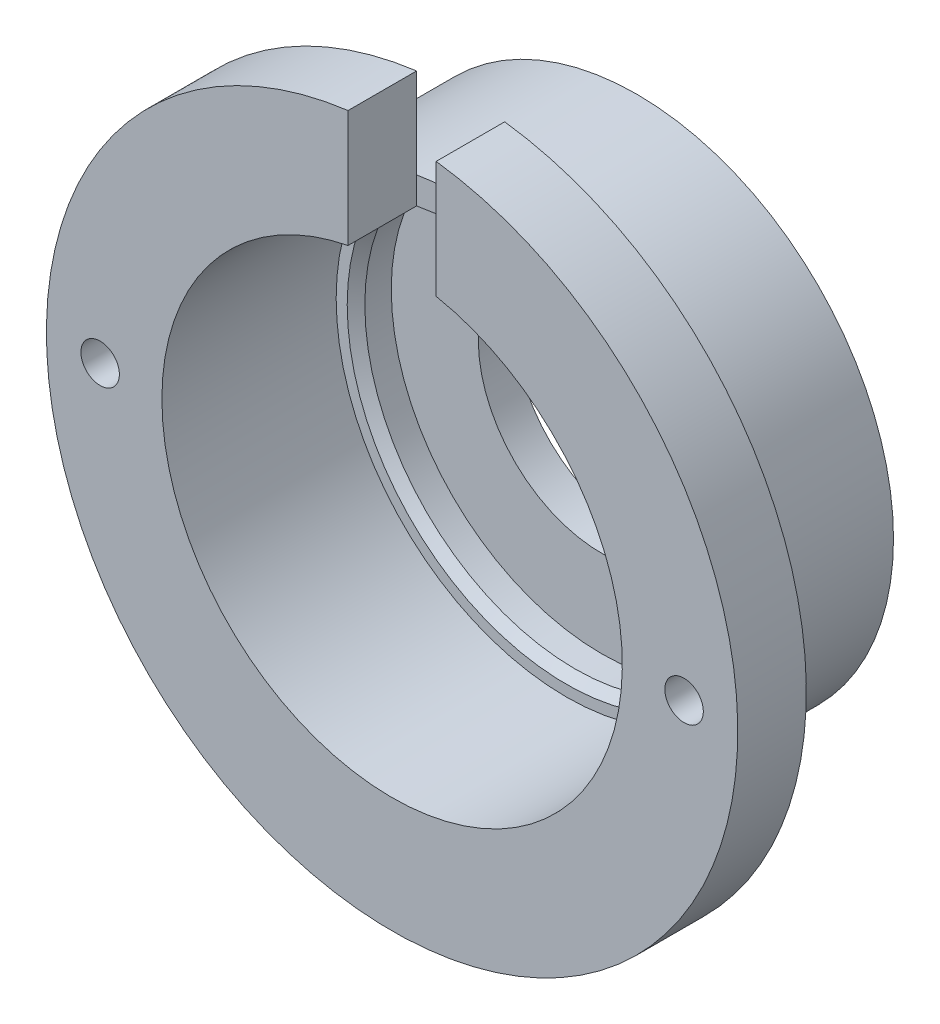
SolidWorks part; units mm, degrees
ref_plane "Front Plane" through (0, 0, 0) normal (0, 0, 1) x (1, 0, 0)
ref_plane "Top Plane" through (0, 0, 0) normal (0, 1, 0) x (1, 0, 0)
ref_plane "Right Plane" through (0, 0, 0) normal (1, 0, 0) x (0, 0, -1)
sketch "Sketch1" plane through (0, 0, 0) normal (0, 1, 0) x (1, 0, 0)
  line L0 (0, 25.4113) -> (0, -24.5124) construction
  line L2 (-7, 4.7005) -> (-19.6178, 4.7005)
  line L3 (-7, 4.7005) -> (-7, 2.7005)
  line L4 (-7, 2.7005) -> (-19.6178, 2.7005)
  line L5 (-19.6178, 4.7005) -> (-19.6178, 2.7005)
  line L6 (-11.938, 2.7005) -> (-19.6178, 2.7005)
  line L7 (-11.938, 2.7005) -> (-11.938, 0.7005)
  line L8 (-11.938, 0.7005) -> (-19.6178, 0.7005)
  line L9 (-19.6178, 2.7005) -> (-19.6178, 0.7005)
  line L10 (-13.0646, 0.7005) -> (-19.6178, 0.7005)
  line L11 (-13.0646, 0.7005) -> (-13.0646, -9.1895)
  line L12 (-13.0646, -9.1895) -> (-19.6178, -9.1895)
  line L13 (-19.6178, 0.7005) -> (-19.6178, -9.1895)
  dimension "D1" = 7
  dimension "D2" = 2
  dimension "D3" = 2
  dimension "D4" = 13.89
  dimension "D5" = 11.938
  dimension "D6" = 6.5532
revolve "Revolve1" add sketch "Sketch1" angle 360 about L0
sketch "Sketch2" plane through (0, 0, -4.7005) normal (0, 0, -1) x (-1, 0, 0)
  line L0 (19.6178, 0) -> (-19.6178, 0) construction
  line L1 (0, 19.4384) -> (0, -19.6178) construction
  circle A0 centre (0, 0) radius 19.6178 construction
  circle A1 centre (0, 0) radius 14.565
  circle A2 centre (0, 0) radius 26.6528
  dimension "D1" = 29.13
extrude "Cut-Extrude1" cut sketch "Sketch2" against normal blind 10
sketch "Sketch4" plane through (0, 0, 5.2995) normal (0, 0, -1) x (-1, 0, 0)
  line L0 (19.6178, 0) -> (-19.6178, 0) construction
  line L1 (0, 18.9883) -> (0, -18.5199) construction
  circle A0 centre (0, 0) radius 19.6178 construction
  circle A1 centre (16.57, 0) radius 1.0922
  circle A2 centre (0, 0) radius 14.565 construction
  circle A3 centre (-16.57, 0) radius 1.0922
  point P11 (14.565, 0)
  point P15 (0, 0)
  dimension "D1" = 2.1844
  dimension "D2" = 16.57
extrude "Cut-Extrude2" cut sketch "Sketch4" against normal through all
chamfer "Chamfer1" distance 0.5 angle 45 1 edges at (-11.938, 0, -0.7005)
sketch "Sketch5" plane through (0, 0, 5.2995) normal (0, 0, -1) x (-1, 0, 0)
  line L0 (0, 0) -> (0, 19.6178) construction
  line L1 (-2.5, 14.565) -> (-2.5, 21.2987)
  line L6 (-2.5, 14.565) -> (2.5, 14.565)
  line L7 (0, 14.565) -> (0, 21.2987)
  line L8 (-2.5, 21.2987) -> (2.5, 21.2987)
  line L9 (2.5, 14.565) -> (2.5, 21.2987)
  circle A0 centre (0, 0) radius 19.6178 construction
  circle A2 centre (0, 0) radius 14.565 construction
  circle M8 centre (0, 0) radius 19.6178
  dimension "D1" = 2.5
extrude "Cut-Extrude3" cut sketch "Sketch5" against normal blind 10 contours L6 L9 L7 M8 | L6 L7 L1 M8
sketch "Sketch6" plane through (0, 14.565, 0) normal (0, 1, 0) x (1, 0, 0)
  line L1 (2.5, -9.1895) -> (-2.5, -9.1895)
  line L2 (2.5, -9.1895) -> (2.5, -5.2995)
  line L3 (2.5, -5.2995) -> (-2.5, -5.2995)
  line L4 (-2.5, -9.1895) -> (-2.5, -5.2995)
extrude "Cut-Extrude4" cut sketch "Sketch6" against normal blind 10
